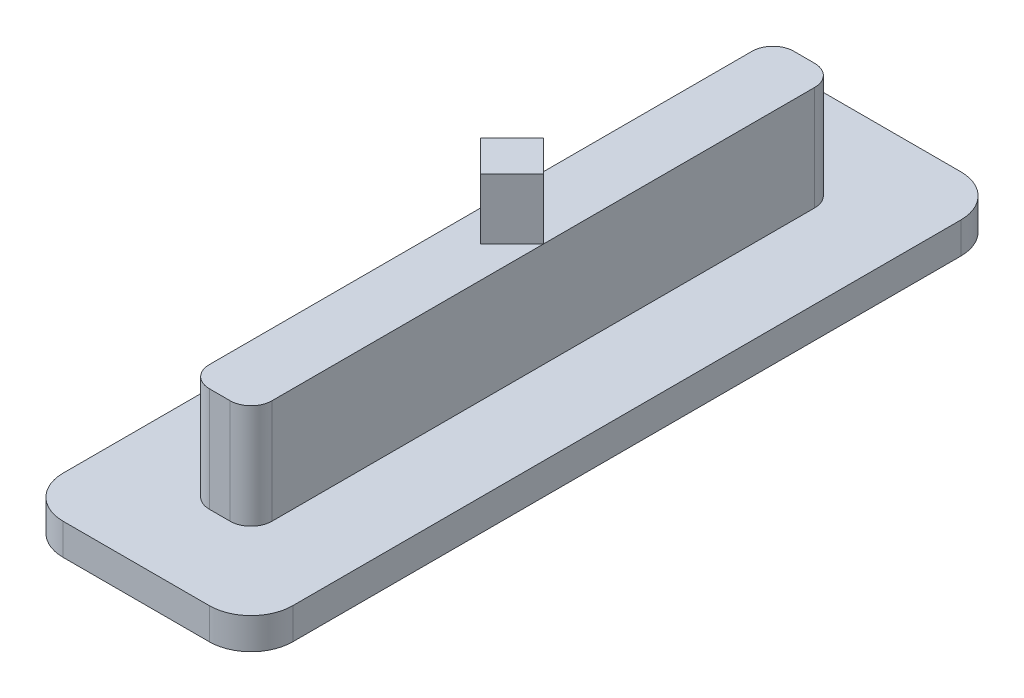
SolidWorks part; units mm, degrees
ref_plane "Спереди" through (0, 0, 0) normal (0, 0, 1) x (1, 0, 0)
ref_plane "Сверху" through (0, 0, 0) normal (0, 1, 0) x (1, 0, 0)
ref_plane "Справа" through (0, 0, 0) normal (1, 0, 0) x (0, 0, -1)
sketch "Эскиз1" plane through (0, 0, 0) normal (0, 1, 0) x (1, 0, 0)
  line L1 (1.5, 14) -> (-1.5, 14)
  line L2 (1.5, 14) -> (1.5, -14)
  line L3 (1.5, -14) -> (-1.5, -14)
  line L4 (-1.5, 14) -> (-1.5, -14)
  line L5 (1.5, 14) -> (-1.5, -14) construction
  line L6 (1.5, -14) -> (-1.5, 14) construction
  point P1 (0, 0)
  dimension "D1" = 28
  dimension "D2" = 3
extrude "Бобышка-Вытянуть1" add sketch "Эскиз1" along normal blind 5
sketch "Эскиз2" plane through (0, 0, 0) normal (0, -1, 0) x (1, 0, 0)
  line L1 (-5.5, -18) -> (5.5, -18)
  line L2 (-5.5, -18) -> (-5.5, 18)
  line L3 (-5.5, 18) -> (5.5, 18)
  line L4 (5.5, -18) -> (5.5, 18)
  line L5 (-5.5, -18) -> (5.5, 18) construction
  line L6 (-5.5, 18) -> (5.5, -18) construction
  point P0 (0, 0)
  dimension "D1" = 36
  dimension "D2" = 11
extrude "Бобышка-Вытянуть2" add sketch "Эскиз2" along normal blind 1.5
fillet "Скругление1" radius 1 4 edges at (1.5, 2.5, -14) (-1.5, 2.5, -14) (1.5, 2.5, 14) (-1.5, 2.5, 14)
fillet "Скругление3" radius 2 4 edges at (5.5, -0.75, 18) (-5.5, -0.75, 18) (5.5, -0.75, -18) (-5.5, -0.75, -18)
sketch "Эскиз3" plane through (0, 5, 0) normal (0, 1, 0) x (1, 0, 0)
  line L8 (-1.5, 0) -> (0, 1.5)
  line L9 (0, 1.5) -> (1.5, 0)
  line L10 (1.5, 0) -> (0, -1.5)
  line L11 (0, -1.5) -> (-1.5, 0)
extrude "Бобышка-Вытянуть3" add sketch "Эскиз3" along normal blind 2.9
